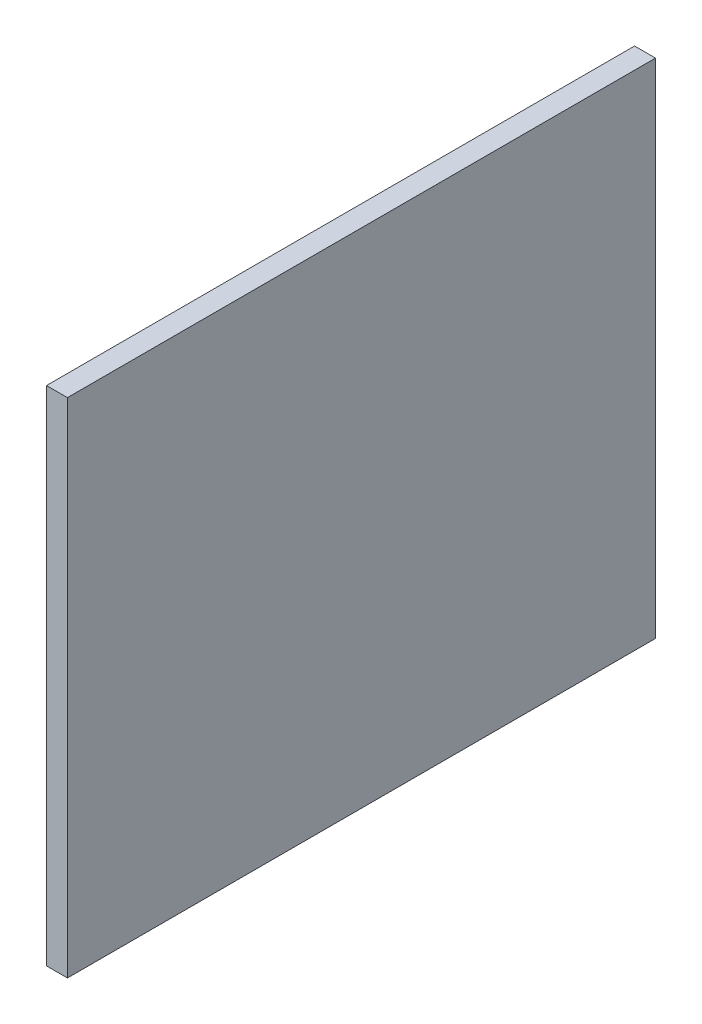
SolidWorks part; units mm, degrees
ref_plane "Front Plane" through (0, 0, 0) normal (0, 0, 1) x (1, 0, 0)
ref_plane "Top Plane" through (0, 0, 0) normal (0, 1, 0) x (1, 0, 0)
ref_plane "Right Plane" through (0, 0, 0) normal (1, 0, 0) x (0, 0, -1)
sketch "Sketch2" plane through (0, 0, 0) normal (1, 0, 0) x (0, 0, -1)
  line L1 (0, 0) -> (89.154, 0)
  line L2 (0, 0) -> (0, 76.2)
  line L3 (0, 76.2) -> (89.154, 76.2)
  line L4 (89.154, 0) -> (89.154, 76.2)
  dimension "D1" = 76.2
  dimension "D2" = 89.154
extrude "Boss-Extrude1" add sketch "Sketch2" along normal blind 3.175
